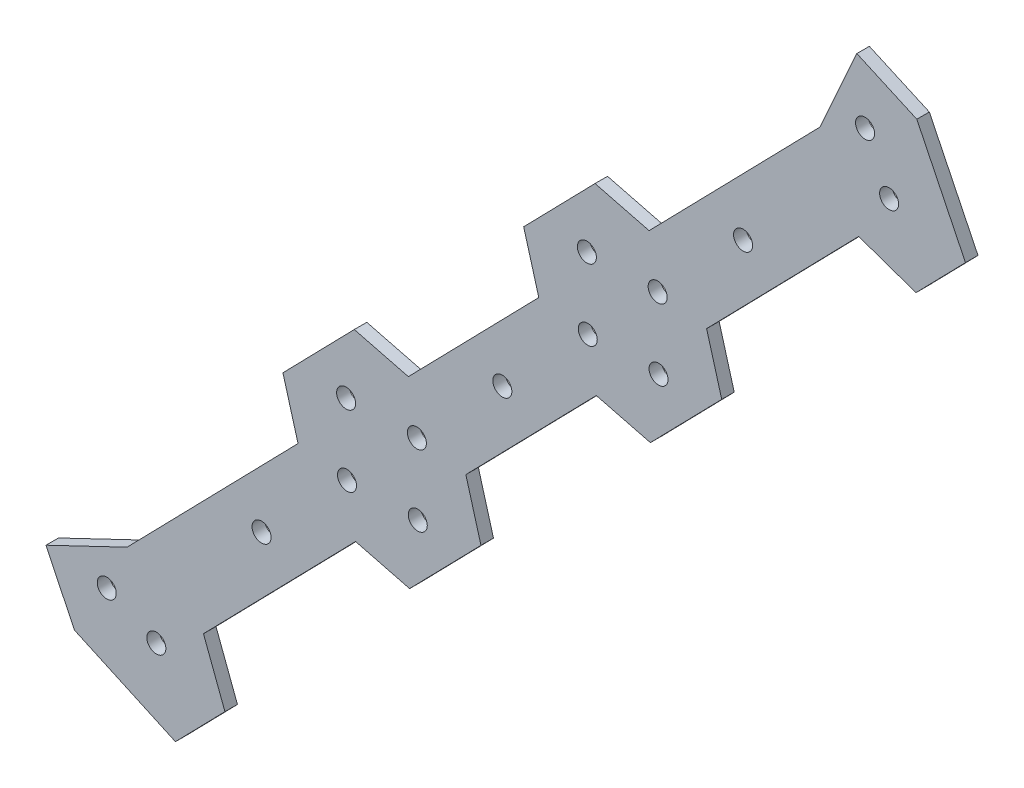
SolidWorks part; units mm, degrees
material "Thornel Mat VMA"
ref_plane "前视基准面" through (0, 0, 0) normal (0, 0, 1) x (1, 0, 0)
ref_plane "上视基准面" through (0, 0, 0) normal (0, 1, 0) x (1, 0, 0)
ref_plane "右视基准面" through (0, 0, 0) normal (1, 0, 0) x (0, 0, -1)
other "Configuration Table"
sketch "草图1" plane through (0, 0, 0) normal (0, 0, 1) x (1, 0, 0)
  line L0 (-130.1126, 209.8938) -> (-122.3328, 193.9287)
  line L2 (-248.6254, 64.4636) -> (-264.7786, 71.845)
  line L3 (-264.7786, 71.845) -> (-269.3159, 81.3216)
  line L4 (-293.8514, 69.5744) -> (-256.354, 87.5275) construction
  line L5 (-269.3159, 81.3216) -> (-256.354, 87.5275)
  line L6 (-244.1441, 81.654) -> (-256.354, 87.5275) construction
  line L7 (-256.354, 87.5275) -> (-145.5813, 201.0828)
  line L8 (-130.1126, 209.8938) -> (-139.6988, 214.1946)
  line L9 (-128.5639, 239.014) -> (-145.5813, 201.0828) construction
  line L10 (-139.6988, 214.1946) -> (-145.5813, 201.0828)
  line L11 (-130.2464, 185.8163) -> (-139.4068, 189.0223)
  line L12 (-139.4068, 189.0223) -> (-8.8144, 143.3168) construction
  line L13 (-145.5813, 201.0828) -> (-139.4068, 189.0223) construction
  line L14 (-139.4068, 189.0223) -> (-244.1441, 81.654)
  line L15 (-244.1441, 81.654) -> (-240.7119, 72.576)
  line L16 (-244.1441, 81.654) -> (-195.2134, -47.7645) construction
  line L17 (-248.6254, 64.4636) -> (-240.7119, 72.576)
  line L18 (-122.3328, 193.9287) -> (-130.2464, 185.8163)
  line L19 (-191.7754, 135.3382) -> (-200.9677, 144.3052)
  line L20 (-196.3716, 139.8217) -> (-157.8843, 179.2757) construction
  line L21 (-177.1279, 159.5487) -> (-171.4013, 153.9624)
  line L22 (-177.1279, 159.5487) -> (-171.5417, 165.2753)
  line L23 (-165.7222, 171.241) -> (-181.5508, 175.2725)
  line L24 (-181.5508, 175.2725) -> (-192.9566, 163.5802)
  line L25 (-192.9566, 163.5802) -> (-188.5337, 147.8564)
  line L26 (-188.5337, 147.8564) -> (-172.705, 143.8249)
  line L27 (-172.705, 143.8249) -> (-161.2992, 155.5172)
  line L28 (-161.2992, 155.5172) -> (-165.7222, 171.241)
  line L29 (-227.021, 108.4024) -> (-231.4439, 124.1262)
  line L30 (-231.4439, 124.1262) -> (-220.0381, 135.8184)
  line L31 (-220.0381, 135.8184) -> (-204.2094, 131.7869)
  line L32 (-204.2094, 131.7869) -> (-199.7865, 116.0631)
  line L33 (-199.7865, 116.0631) -> (-211.1923, 104.3708)
  line L34 (-211.1923, 104.3708) -> (-227.021, 108.4024)
  circle A0 centre (-157.8843, 179.2757) radius 1.52
  circle A1 centre (-171.4013, 153.9624) radius 1.52
  circle A2 centre (-196.3716, 139.8217) radius 1.52
  circle A3 centre (-177.1279, 159.5487) radius 14.1457 construction
  circle A4 centre (-171.5417, 165.2753) radius 1.52
  circle A5 centre (-182.7142, 153.8221) radius 1.52
  circle A6 centre (-182.8545, 165.135) radius 1.52
  circle A7 centre (-134.5389, 196.6796) radius 1.52
  circle A8 centre (-138.3873, 204.5128) radius 1.52
  circle A9 centre (-209.8886, 114.5084) radius 1.52
  circle A10 centre (-210.0289, 125.8212) radius 1.52
  circle A11 centre (-221.3418, 125.6809) radius 1.52
  circle A12 centre (-221.2015, 114.368) radius 1.52
  circle A13 centre (-234.8588, 100.3676) radius 1.52
  circle A14 centre (-251.6783, 76.5977) radius 1.52
  circle A15 centre (-259.6045, 80.2507) radius 1.52
  point P78 (0, 0)
  point P79 (0, 0)
  dimension "D1" = 8
  dimension "D2" = 8
extrude "凸台-拉伸1" add sketch "草图1" along normal blind 2
